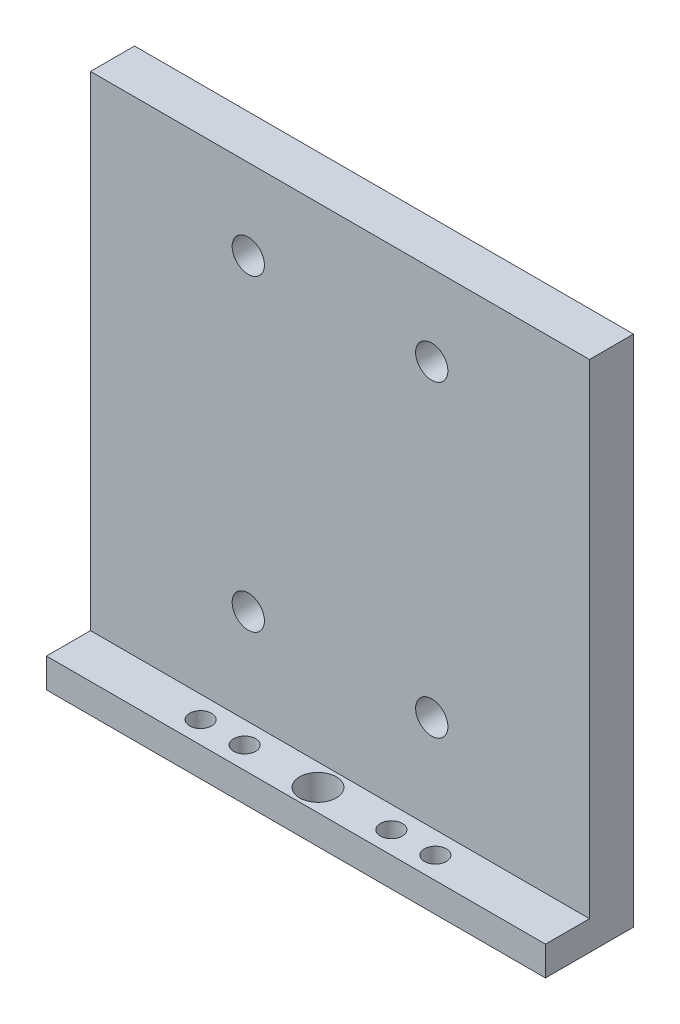
SolidWorks part; units mm, degrees
material "1060 Alloy"
ref_plane "Front Plane" through (0, 0, 0) normal (0, 0, 1) x (1, 0, 0)
ref_plane "Top Plane" through (0, 0, 0) normal (0, 1, 0) x (1, 0, 0)
ref_plane "Right Plane" through (0, 0, 0) normal (1, 0, 0) x (0, 0, -1)
sketch "Sketch1" plane through (0, 0, 0) normal (1, 0, 0) x (0, 0, -1)
  line L0 (0, 0) -> (6, 0)
  line L1 (6, 0) -> (6, 35)
  line L2 (6, 35) -> (3, 35)
  line L3 (3, 35) -> (3, 2)
  line L4 (3, 2) -> (0, 2)
  line L5 (0, 2) -> (0, 0)
  line L7 (-16.05, 5) -> (3, 5) construction
  line L8 (-16.05, 5) -> (-16.05, 35) construction
  line L9 (-16.05, 35) -> (3, 35) construction
  line L10 (3, 5) -> (3, 35) construction
  dimension "D1" = 2
  dimension "D2" = 3
  dimension "D3" = 3
  dimension "D4" = 30
  dimension "D5" = 19.05
  dimension "D6" = 3
extrude "Boss-Extrude1" add sketch "Sketch1" along normal blind 34
sketch "Sketch2" plane through (0, 0, -3) normal (0, 0, 1) x (1, 0, 0)
  line L0 (17, 19) -> (17, 2) construction
  line L1 (10.75, 8.5) -> (23.25, 8.5) construction
  line L2 (10.75, 8.5) -> (10.75, 29.5) construction
  line L3 (10.75, 29.5) -> (23.25, 29.5) construction
  line L4 (23.25, 8.5) -> (23.25, 29.5) construction
  line L5 (10.75, 8.5) -> (23.25, 29.5) construction
  line L6 (10.75, 29.5) -> (23.25, 8.5) construction
  line L7 (34, 2) -> (0, 2) construction
  line L9 (2, 4) -> (32, 4) construction
  line L10 (2, 4) -> (2, 34) construction
  line L11 (2, 34) -> (32, 34) construction
  line L12 (32, 4) -> (32, 34) construction
  line L13 (2, 4) -> (32, 34) construction
  line L14 (2, 34) -> (32, 4) construction
  circle A0 centre (23.25, 29.5) radius 1.1
  circle A1 centre (10.75, 29.5) radius 1.1
  circle A2 centre (10.75, 8.5) radius 1.1
  circle A3 centre (23.25, 8.5) radius 1.1
  point P0 (17, 19)
  dimension "D4" = 2.2
  dimension "D1" = 12.5
  dimension "D2" = 30
  dimension "D3" = 2
  dimension "D5" = 21
extrude "Cut-Extrude1" cut sketch "Sketch2" against normal through all
sketch "Sketch3" plane through (0, 2, 0) normal (0, 1, 0) x (1, 0, 0)
  line L0 (9, 1.5) -> (12, 1.5) construction
  line L1 (12, 1.5) -> (17, 1.5) construction
  line L2 (17, 1.5) -> (22, 1.5) construction
  line L3 (22, 1.5) -> (25, 1.5) construction
  line L4 (17, 1.5) -> (17, 0) construction
  line L6 (25, 1.5) -> (34, 1.5) construction
  line L7 (34, 3) -> (34, 0) construction
  line L8 (34, 0) -> (0, 0) construction
  circle A0 centre (17, 1.5) radius 1.25
  circle A1 centre (22, 1.5) radius 0.75
  circle A2 centre (25, 1.5) radius 0.75
  circle A3 centre (12, 1.5) radius 0.75
  circle A4 centre (9, 1.5) radius 0.75
  dimension "D1" = 2.5
  dimension "D2" = 1.5
  dimension "D3" = 5
  dimension "D4" = 3
extrude "Cut-Extrude2" cut sketch "Sketch3" against normal through all
